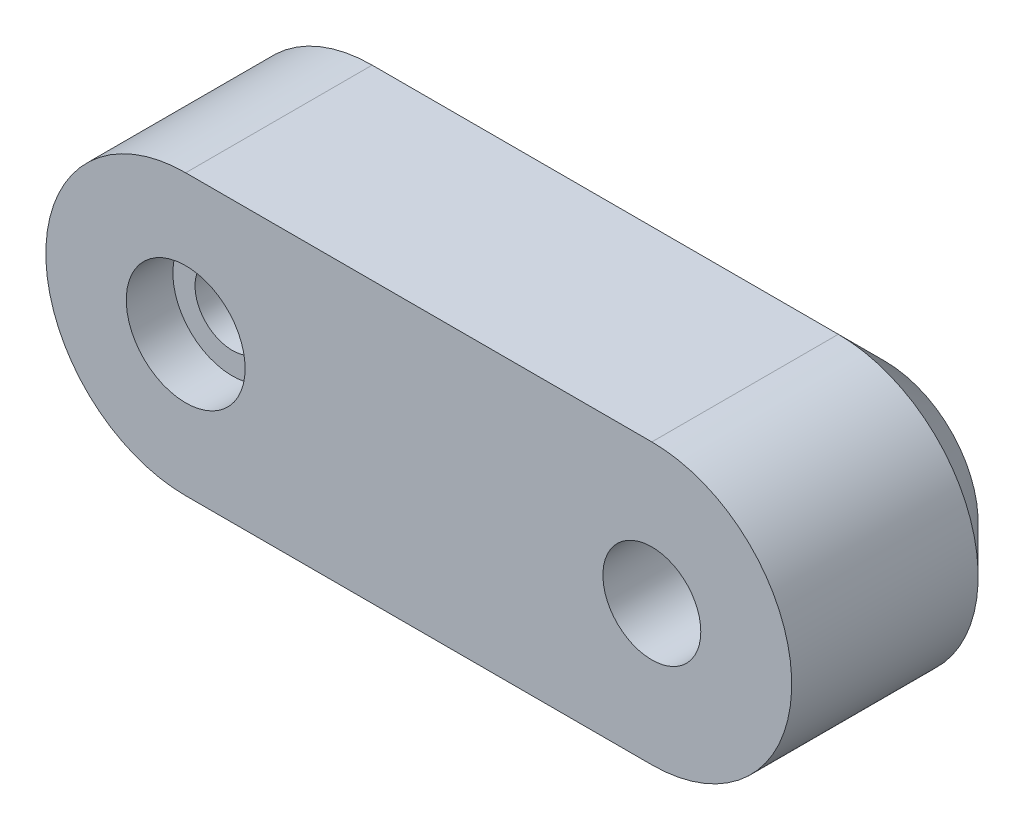
SolidWorks part; units mm, degrees
ref_plane "前视基准面" through (0, 0, 0) normal (0, 0, 1) x (1, 0, 0)
ref_plane "上视基准面" through (0, 0, 0) normal (0, 1, 0) x (1, 0, 0)
ref_plane "右视基准面" through (0, 0, 0) normal (1, 0, 0) x (0, 0, -1)
sketch "草图1" plane through (0, 0, 0) normal (0, 0, 1) x (1, 0, 0)
  line L0 (0, 0) -> (20, 0) construction
  line L1 (0, 6) -> (20, 6)
  line L2 (0, -6) -> (20, -6)
  arc A0 (0, 6) -> (0, -6) centre (0, 0) ccw
  arc A1 (20, -6) -> (20, 6) centre (20, 0) ccw
  point P3 (10, 0)
  dimension "D2" = 6
  dimension "D1" = 20
extrude "凸台-拉伸1" add sketch "草图1" along normal blind 10
sketch "草图2" plane through (0, 0, 0) normal (0, 1, 0) x (1, 0, 0)
  line L0 (0, 0) -> (-2.55, 0)
  line L1 (0, 0) -> (-6, 0) construction
  line L2 (-2.55, 0) -> (-2.55, -5)
  line L3 (-2.55, -5) -> (-1.6, -5)
  line L4 (-1.6, -5) -> (-1.6, -8)
  line L5 (-1.6, -8) -> (-2.55, -8)
  line L6 (-2.55, -8) -> (-2.55, -10)
  line L7 (-6, -10) -> (0, -10) construction
  line L8 (-2.55, -10) -> (0, -10)
  line L9 (0, -10) -> (0, 0)
  dimension "D1" = 2.55
  dimension "D2" = 3
  dimension "D3" = 5
  dimension "D4" = 1.6
  dimension "D5" = 2.55
revolve "切除-旋转1" cut sketch "草图2" angle 360 about L9
sketch "草图3" plane through (0, 0, 0) normal (0, 1, 0) x (1, 0, 0)
  line L0 (20, 0) -> (17.42, 0)
  line L1 (20, 0) -> (0, 0) construction
  line L2 (17.42, 0) -> (17.42, -5)
  line L3 (17.42, -5) -> (17.9, -5)
  line L4 (17.9, -5) -> (17.9, -10)
  line L5 (20, -10) -> (0, -10) construction
  line L6 (17.9, -10) -> (20, -10)
  line L7 (20, -10) -> (20, 0)
  dimension "D1" = 2.58
  dimension "D2" = 5
  dimension "D3" = 2.1
revolve "切除-旋转2" cut sketch "草图3" angle 360 about L7
chamfer "倒角1" distance 2 angle 45 4 edges at (10, 6, 0) (-6, 0, 0) (26, 0, 0) (10, -6, 0)
sketch "草图4" plane through (0, 0, 0) normal (0, 0, -1) x (-1, 0, 0)
  line L0 (0, -6) -> (-20, -6) construction
  line L1 (-23.3486, 0) -> (-21.6743, -2.9)
  line L2 (-21.6743, -2.9) -> (-18.3257, -2.9)
  line L3 (-18.3257, -2.9) -> (-16.6514, 0)
  line L4 (-16.6514, 0) -> (-18.3257, 2.9)
  line L5 (-18.3257, 2.9) -> (-21.6743, 2.9)
  line L6 (-21.6743, 2.9) -> (-23.3486, 0)
  circle A0 centre (-20, 0) radius 2.9 construction
  dimension "D1" = 5.8
extrude "切除-拉伸1" cut sketch "草图4" against normal blind 4
